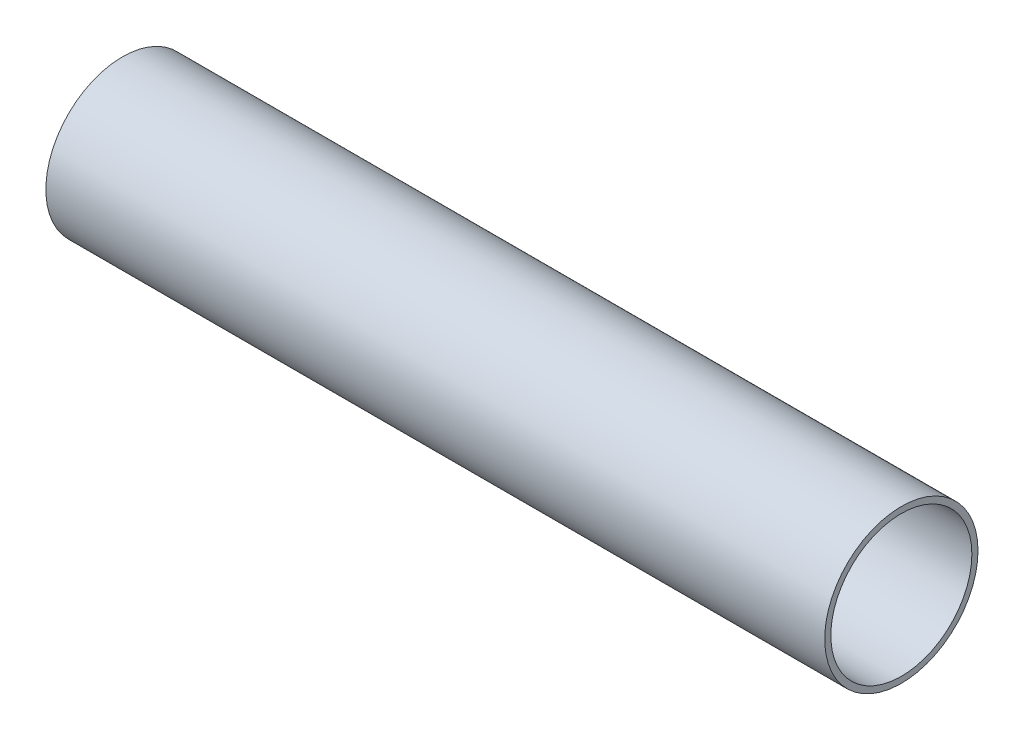
SolidWorks part; units mm, degrees
ref_plane "Front Plane" through (0, 0, 0) normal (0, 0, 1) x (1, 0, 0)
ref_plane "Top Plane" through (0, 0, 0) normal (0, 1, 0) x (1, 0, 0)
ref_plane "Right Plane" through (0, 0, 0) normal (1, 0, 0) x (0, 0, -1)
sketch "Sketch1" plane through (0, 0, 0) normal (1, 0, 0) x (0, 0, -1)
  circle A0 centre (0, 0) radius 12.5
  circle A1 centre (0, 0) radius 11.5
  dimension "D1" = 25
  dimension "D2" = 1
extrude "Boss-Extrude1" add sketch "Sketch1" along normal blind 127
